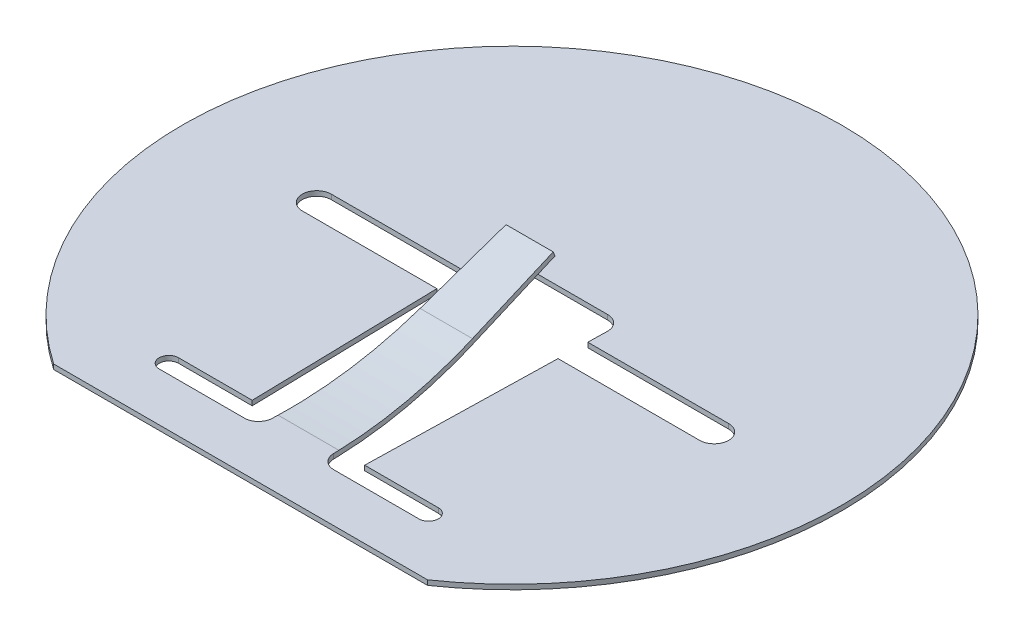
SolidWorks part; units mm, degrees
material "ABS PC"
ref_plane "Front Plane" through (0, 0, 0) normal (0, 0, 1) x (1, 0, 0)
ref_plane "Top Plane" through (0, 0, 0) normal (0, 1, 0) x (1, 0, 0)
ref_plane "Right Plane" through (0, 0, 0) normal (1, 0, 0) x (0, 0, -1)
sketch "Sketch1" plane through (0, 0, 0) normal (0, 1, 0) x (1, 0, 0)
  line L0 (4.8218, -7) -> (-4.8218, -7)
  line L1 (-55, 0) -> (55, 0) construction
  line L2 (1.5625, -0.375) -> (5.215, -0.375)
  line L3 (-5.035, 0.375) -> (-1.5798, 0.375)
  line L4 (-5.035, -0.375) -> (-1.5625, -0.375)
  line L5 (0, -55) -> (0, 55) construction
  line L6 (-1.5625, -0.375) -> (-1.45, -5.25)
  line L7 (-1.2162, 1.25) -> (1.2162, 1.25)
  line L8 (1.5625, -0.375) -> (1.45, -5.25)
  line L9 (1.5798, 0.375) -> (5.215, 0.375)
  line L10 (-1.5911, 0.8663) -> (-1.5798, 0.375)
  line L11 (-1.45, -5.25) -> (-3.35, -5.25)
  line L12 (1.5911, 0.8663) -> (1.5798, 0.375)
  line L13 (1.45, -5.25) -> (3.35, -5.25)
  line L14 (-3.35, -5.75) -> (3.35, -5.75)
  arc A0 (4.8218, -7) -> (-4.8218, -7) centre (0, 0) ccw
  arc A1 (-5.035, 0.375) -> (-5.035, -0.375) centre (-5.035, 0) ccw
  arc A2 (5.215, -0.375) -> (5.215, 0.375) centre (5.215, 0) ccw
  arc A3 (3.35, -5.25) -> (3.35, -5.75) centre (3.35, -5.5) cw
  arc A4 (-3.35, -5.25) -> (-3.35, -5.75) centre (-3.35, -5.5) ccw
  arc A5 (-1.5911, 0.8663) -> (-1.2162, 1.25) centre (-1.2162, 0.875) cw
  arc A6 (1.2162, 1.25) -> (1.5911, 0.8663) centre (1.2162, 0.875) cw
  point P8 (0.09, 0)
  point P29 (-1.6, 1.25)
  point P34 (1.6, 1.25)
  dimension "D1" = 8.5
  dimension "D7" = 1.6
  dimension "D10" = 0.375
  dimension "D9" = 2.9
  dimension "D2" = 7
  dimension "D3" = 0.75
  dimension "D4" = 10.25
  dimension "D5" = 5.215
  dimension "D6" = 1.25
  dimension "D8" = 1.6
  dimension "D11" = 6.7
  dimension "D12" = 0.5
  dimension "D13" = 3.35
  dimension "D14" = 5.75
  dimension "D15" = 1.45
extrude "Extrude1" add sketch "Sketch1" along normal blind 0.125
sketch "Sketch2" plane through (0, 0, 0) normal (1, 0, 0) x (0, 0, -1)
  line L0 (-1.6504, 0.6703) -> (0.5, 1.5)
  line L1 (0, 0.7808) -> (0, -0.7808) construction
  line L2 (8.525, 0) -> (-8.525, 0) construction
  line L3 (-5.75, 0) -> (-5.25, 0)
  arc A1 (-1.6504, 0.6703) -> (-5.25, 0) centre (-5.25, 10) cw
  dimension "D4" = 0.5
  dimension "D1" = 10
  dimension "D2" = 0.5
  dimension "D3" = 1.5
  dimension "D5" = 5.75
ref_plane "Plane1" through (0, 0, 5.75) normal (0, 0, -1) x (-1, 0, 0)
sketch "Sketch3" plane through (0, 0, 5.75) normal (0, 0, -1) x (-1, 0, 0)
  line L1 (-0.8, 0.125) -> (0.8, 0.125)
  line L2 (-0.8, 0.125) -> (-0.8, 0)
  line L3 (-0.8, 0) -> (0.8, 0)
  line L4 (0.8, 0.125) -> (0.8, 0)
  line L6 (0, 0.7808) -> (0, -0.7808) construction
  line L7 (8.525, 0) -> (-8.525, 0) construction
  dimension "D1" = 0.125
  dimension "D2" = 1.6
  dimension "D3" = 0.8
sweep "Sweep2" add profiles "Sketch3" path "Sketch2"
sketch "Sketch5" plane through (0, 0, 0) normal (0, 1, 0) x (1, 0, 0)
  line L0 (-0.6, 0.75) -> (-0.8, -5.75)
  line L1 (-0.8, -5.75) -> (-1.2, -5.75)
  line L2 (-1.2, -5.75) -> (-1.2, 1)
  line L3 (-1.2, 1) -> (1.2, 1)
  line L4 (1.2, 1) -> (1.2, -5.75)
  line L5 (1.2, -5.75) -> (0.8, -5.75)
  line L6 (0.8, -5.75) -> (0.6, 0.75)
  line L7 (0.6, 0.75) -> (-0.6, 0.75)
  line L8 (-0.5626, 0) -> (0.5626, 0) construction
  line L9 (0, -0.5626) -> (0, 0.5626) construction
  dimension "D1" = 0.75
  dimension "D2" = 0.6
  dimension "D3" = 1.2
  dimension "D4" = 5.75
  dimension "D5" = 1.6
  dimension "D6" = 0.8
  dimension "D7" = 2.4
  dimension "D8" = 1.2
  dimension "D9" = 1
extrude "Extrude2" cut sketch "Sketch5" along normal through all
fillet "Fillet3" radius 0.365 2 edges at (0.8, 0.0625, 5.75) (-0.8, 0.0625, 5.75)
